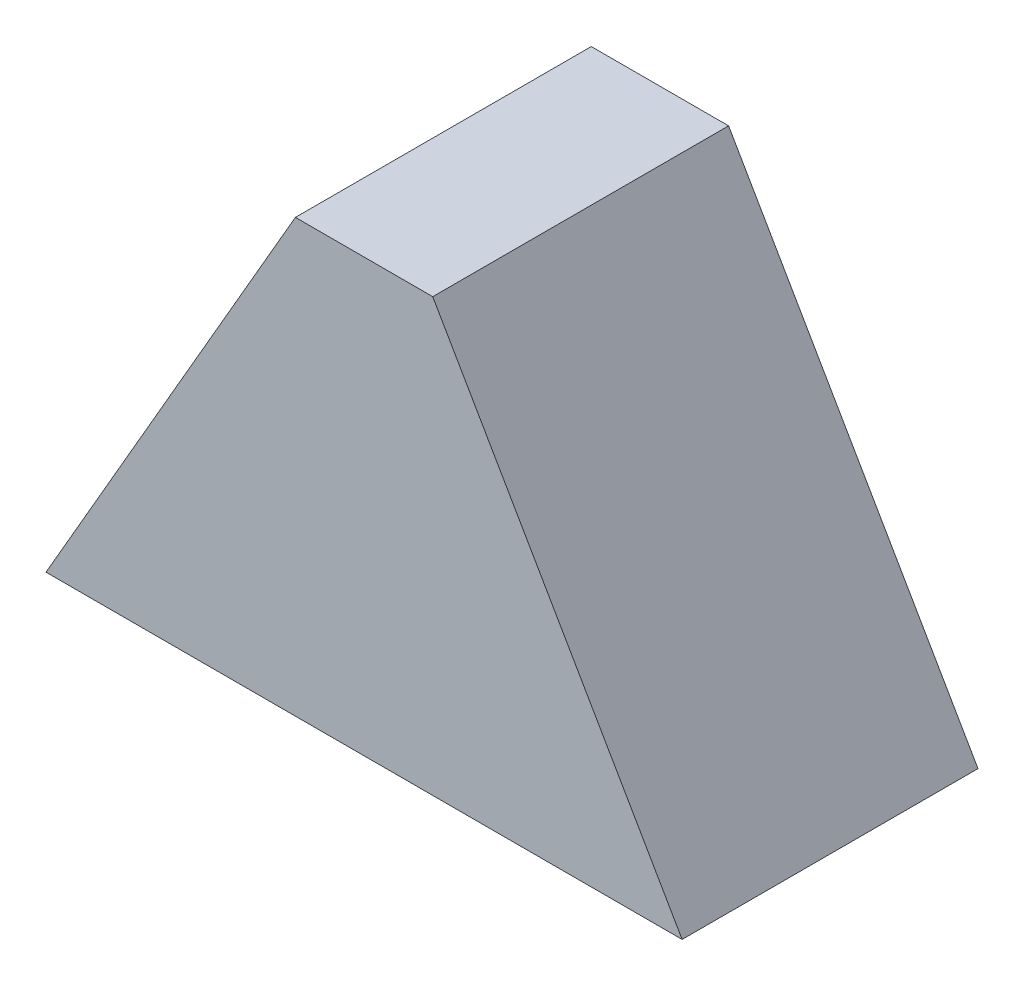
SolidWorks part; units mm, degrees
ref_plane "前视基准面" through (0, 0, 0) normal (0, 0, 1) x (1, 0, 0)
ref_plane "上视基准面" through (0, 0, 0) normal (0, 1, 0) x (1, 0, 0)
ref_plane "右视基准面" through (0, 0, 0) normal (1, 0, 0) x (0, 0, -1)
sketch "草图1" plane through (0, 0, 0) normal (0, 0, 1) x (1, 0, 0)
  line L0 (0, 0) -> (168.5863, 292)
  line L1 (168.5863, 292) -> (261.4137, 292)
  line L2 (261.4137, 292) -> (430, 0)
  line L3 (430, 0) -> (0, 0)
  line L4 (215, 0) -> (215, 292) construction
  point P7 (215, 292)
  dimension "D1" = 430
  dimension "D2" = 292
  dimension "D3" = 60
extrude "凸台-拉伸1" add sketch "草图1" along normal blind 200
